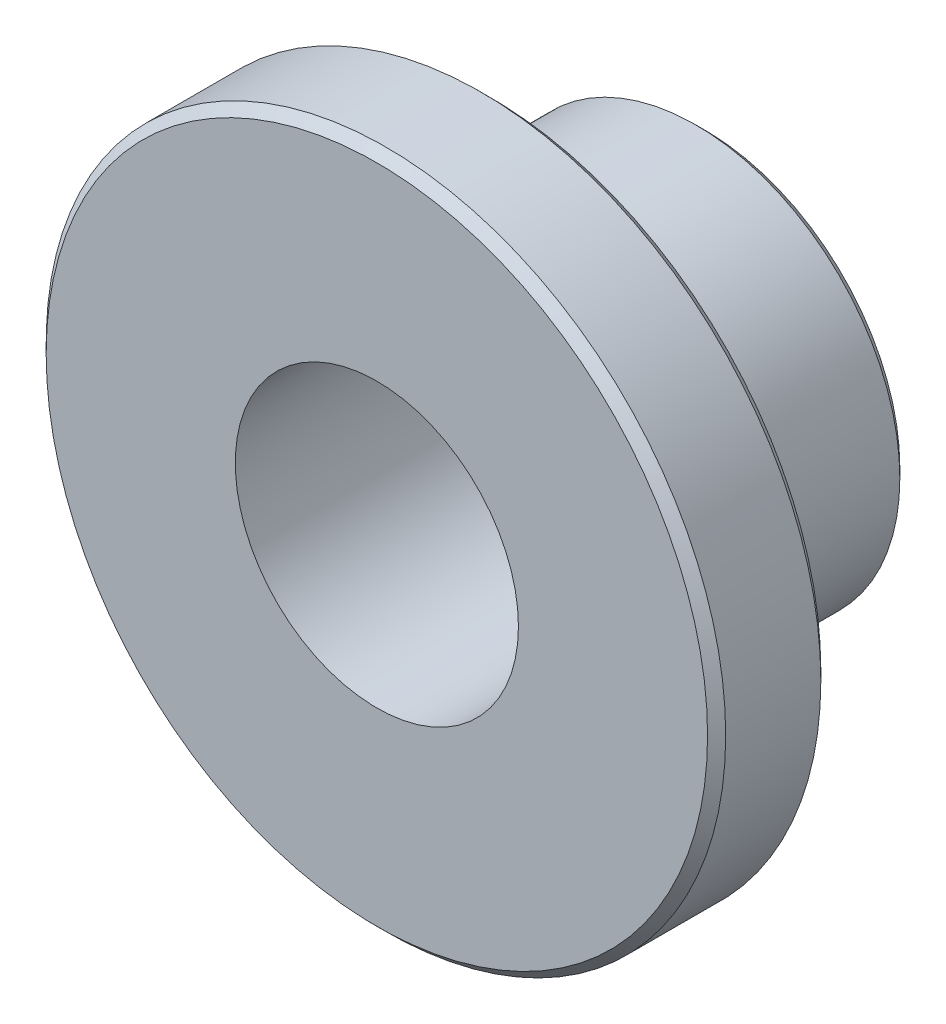
SolidWorks part; units mm, degrees
ref_plane "Front" through (0, 0, 0) normal (0, 0, 1) x (1, 0, 0)
ref_plane "Top" through (0, 0, 0) normal (0, 1, 0) x (1, 0, 0)
ref_plane "Right" through (0, 0, 0) normal (1, 0, 0) x (0, 0, -1)
sketch "Sketch1" plane through (0, 0, 0) normal (0, 0, 1) x (1, 0, 0)
  circle A0 centre (0, 0) radius 5.715
  circle A1 centre (0, 0) radius 3.9688
  dimension "D1" = 7.9375
  dimension "D2" = 11.43
extrude "Boss-Extrude1" add sketch "Sketch1" along normal mid plane 9.2
sketch "Sketch2" plane through (0, 0, 4.6) normal (0, 0, 1) x (1, 0, 0)
  circle A0 centre (0, 0) radius 9.525
  circle A1 centre (0, 0) radius 5.715 construction
  circle A2 centre (0, 0) radius 5.715
  dimension "D1" = 19.05
extrude "Boss-Extrude2" add sketch "Sketch2" against normal blind 3.175
chamfer "Chamfer2" distance 0.254 angle 45 3 edges at (5.715, 0, -4.6) (9.525, 0, 1.425) (9.525, 0, 4.6)
